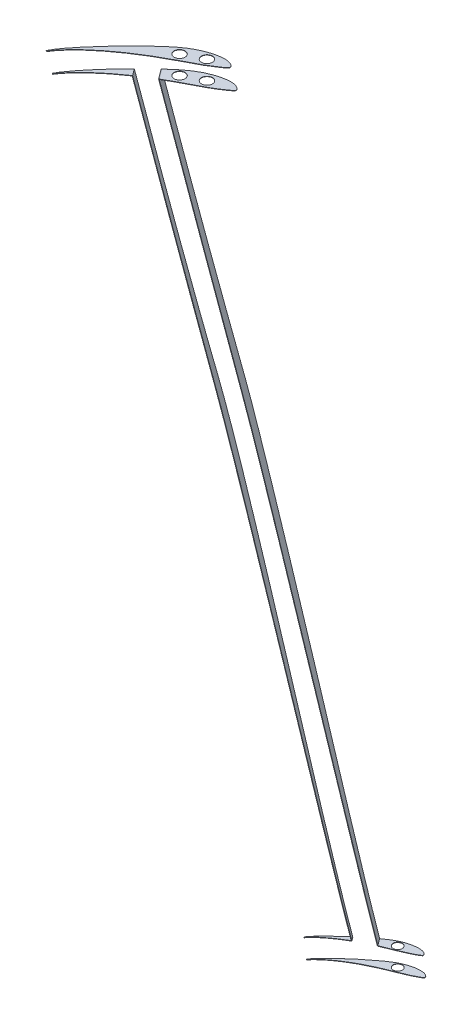
SolidWorks part; units mm, degrees
material "Thornel Mat VMA"
ref_plane "Płaszczyzna przednia" through (0, 0, 0) normal (0, 0, 1) x (1, 0, 0)
ref_plane "Płaszczyzna górna" through (0, 0, 0) normal (0, 1, 0) x (1, 0, 0)
ref_plane "Płaszczyzna prawa" through (0, 0, 0) normal (1, 0, 0) x (0, 0, -1)
sketch "Szkic1" plane through (0, 700, 0) normal (0, 1, 0) x (1, 0, 0)
  line L1 (-469.1512, -367.5434) -> (-468.754, -367.81)
  line L2 (-469.1512, -367.5434) -> (-468.754, -367.81)
  spline S1 degree 3 poles (2934.6392, 1730.5691) (-451.467, -472.6179) (-487.4852, -393.6485) (-466.9474, -365.123) (-465.4843, -363.3061) (-463.7563, -361.3596) (-461.7776, -359.314) (-459.5701, -357.2008) (-457.1553, -355.0511) (-454.5622, -352.8909) (-451.8199, -350.7459) (-448.9593, -348.6392) (-446.0148, -346.5897) (-443.0211, -344.6138) (-440.0111, -342.7277) (-437.0217, -340.9383) (-434.0854, -339.2548) (-431.2362, -337.6806) (-428.5045, -336.2174) (-425.9206, -334.863) (-423.5124, -333.6111) (-421.2981, -332.4595) (-419.3013, -331.3589) (-417.5203, -330.2935) (-415.9266, -329.301) (-414.5247, -328.3906) (-413.33, -327.5701) (-412.3464, -326.8605) (-411.611, -326.237) (-411.0798, -325.7733) (-410.823, -325.2531) (-411.0233, -324.7717) (-411.3436, -324.3272) (-411.8418, -323.8959) (-412.4803, -323.5065) (-413.2563, -323.1781) (-414.1577, -322.9224) (-415.1876, -322.7716) (-416.3391, -322.7288) (-417.6073, -322.7797) (-418.9822, -322.9364) (-420.4518, -323.2021) (-422.0055, -323.5786) (-423.6313, -324.0737) (-425.3194, -324.6838) (-427.0559, -325.415) (-428.8294, -326.2693) (-430.6234, -327.2643) (-432.439, -328.3995) (-434.2696, -329.6972) (-436.1216, -331.1507) (-438.019, -332.7225) (-439.9443, -334.4145) (-441.896, -336.2055) (-443.8686, -338.0781) (-445.856, -340.0094) (-447.8437, -341.9814) (-449.8187, -343.9734) (-451.762, -345.9737) (-453.6586, -347.9688) (-455.4966, -349.9456) (-457.2622, -351.894) (-458.9469, -353.8003) (-460.5389, -355.6542) (-462.0306, -357.4425) (-463.4128, -359.1548) (-464.6773, -360.7805) (-465.8172, -362.31) (-466.8274, -363.7332) (-467.7019, -365.0426) (-468.4374, -366.23) (-480.5946, -387.92) (-453.6741, -427.6699) (2877.8906, -2556.2502) knots -0.615528 -0.615528 -0.615528 -0.615528 0.028864 0.041831 0.056714 0.073341 0.091508 0.111022 0.131662 0.153208 0.175433 0.19811 0.221011 0.243906 0.266573 0.28881 0.310405 0.331178 0.350944 0.369556 0.386865 0.402753 0.417196 0.43038 0.442363 0.453032 0.462284 0.470026 0.476177 0.48065 0.483553 0.486421 0.489953 0.494097 0.498851 0.504197 0.510125 0.516691 0.524012 0.532092 0.540898 0.550403 0.560581 0.571396 0.582828 0.59483 0.607347 0.620384 0.633969 0.6482 0.663194 0.678899 0.695227 0.712113 0.729459 0.747143 0.76501 0.782905 0.800688 0.818242 0.835449 0.852212 0.86843 0.884009 0.898855 0.912882 0.926011 0.938167 0.94929 0.959322 0.968217 0.975948 1.433508 1.433508 1.433508 1.433508 only from (-468.754, -367.81) to (-469.1512, -367.5434)
  spline S2 degree 3 poles (-468.754, -367.81) (-468.5693, -367.4945) (-468.0116, -366.601) (-466.9474, -365.123) (-465.4843, -363.3061) (-463.7563, -361.3596) (-461.7776, -359.314) (-459.5701, -357.2008) (-457.1553, -355.0511) (-454.5622, -352.8909) (-451.8199, -350.7459) (-448.9593, -348.6392) (-446.0148, -346.5897) (-443.0211, -344.6138) (-440.0111, -342.7277) (-437.0217, -340.9383) (-434.0854, -339.2548) (-431.2362, -337.6806) (-428.5045, -336.2174) (-425.9206, -334.863) (-423.5124, -333.6111) (-421.2981, -332.4595) (-419.3013, -331.3589) (-417.5203, -330.2935) (-415.9266, -329.301) (-414.5247, -328.3906) (-413.33, -327.5701) (-412.3464, -326.8605) (-411.611, -326.237) (-411.0798, -325.7733) (-410.823, -325.2531) (-411.0233, -324.7717) (-411.3436, -324.3272) (-411.8418, -323.8959) (-412.4803, -323.5065) (-413.2563, -323.1781) (-414.1577, -322.9224) (-415.1876, -322.7716) (-416.3391, -322.7288) (-417.6073, -322.7797) (-418.9822, -322.9364) (-420.4518, -323.2021) (-422.0055, -323.5786) (-423.6313, -324.0737) (-425.3194, -324.6838) (-427.0559, -325.415) (-428.8294, -326.2693) (-430.6234, -327.2643) (-432.439, -328.3995) (-434.2696, -329.6972) (-436.1216, -331.1507) (-438.019, -332.7225) (-439.9443, -334.4145) (-441.896, -336.2055) (-443.8686, -338.0781) (-445.856, -340.0094) (-447.8437, -341.9814) (-449.8187, -343.9734) (-451.762, -345.9737) (-453.6586, -347.9688) (-455.4966, -349.9456) (-457.2622, -351.894) (-458.9469, -353.8003) (-460.5389, -355.6542) (-462.0306, -357.4425) (-463.4128, -359.1548) (-464.6773, -360.7805) (-465.8172, -362.31) (-466.8274, -363.7332) (-467.7019, -365.0426) (-468.4374, -366.23) (-468.8993, -367.0541) (-469.1182, -367.4785) (-469.1512, -367.5434) knots 0.021883 0.021883 0.021883 0.021883 0.028864 0.041831 0.056714 0.073341 0.091508 0.111022 0.131662 0.153208 0.175433 0.19811 0.221011 0.243906 0.266573 0.28881 0.310405 0.331178 0.350944 0.369556 0.386865 0.402753 0.417196 0.43038 0.442363 0.453032 0.462284 0.470026 0.476177 0.48065 0.483553 0.486421 0.489953 0.494097 0.498851 0.504197 0.510125 0.516691 0.524012 0.532092 0.540898 0.550403 0.560581 0.571396 0.582828 0.59483 0.607347 0.620384 0.633969 0.6482 0.663194 0.678899 0.695227 0.712113 0.729459 0.747143 0.76501 0.782905 0.800688 0.818242 0.835449 0.852212 0.86843 0.884009 0.898855 0.912882 0.926011 0.938167 0.94929 0.959322 0.968217 0.975948 0.977339 0.977339 0.977339 0.977339
  dimension "D1" = 0
extrude "Dodanie-wyciągnięcie1" add sketch "Szkic1" along normal blind 0.2
sketch "Szkic2" plane through (0, 690, 0) normal (0, -1, 0) x (1, 0, 0)
  line L0 (-435.1547, 340.1136) -> (-439.1678, 334.7049) construction
  line L1 (-466.5168, 366.7553) -> (-466.9139, 366.4887) construction
  line L2 (-446.602, 341.9323) -> (-443.8693, 345.6152) construction
  line L3 (-435.1547, 340.1136) -> (-439.1678, 334.7049)
  line L4 (-466.5168, 366.7553) -> (-466.9139, 366.4887)
  line L5 (-446.602, 341.9323) -> (-443.8693, 345.6152)
  spline S0 degree 3 poles (-2529.6654, -1804.7759) (-503.5039, 558.2909) (-512.0423, 398.6848) (-435.7818, 331.6679) (-433.8844, 330.096) (-432.0324, 328.6425) (-430.2018, 327.3448) (-428.3861, 326.2096) (-426.5921, 325.2146) (-424.8187, 324.3603) (-423.0822, 323.6291) (-421.394, 323.019) (-419.7682, 322.5239) (-418.2145, 322.1474) (-416.745, 321.8817) (-415.3701, 321.725) (-414.1018, 321.6741) (-412.9503, 321.717) (-411.9205, 321.8677) (-411.0191, 322.1234) (-410.2431, 322.4518) (-409.6046, 322.8412) (-409.1064, 323.2725) (-408.7861, 323.717) (-408.5857, 324.1984) (-408.8425, 324.7186) (-409.3738, 325.1823) (-410.1092, 325.8058) (-411.0927, 326.5154) (-412.2874, 327.3359) (-413.6894, 328.2463) (-415.283, 329.2388) (-417.064, 330.3042) (-419.0609, 331.4049) (-421.2751, 332.5564) (-423.6833, 333.8083) (-426.2672, 335.1627) (-428.9989, 336.6259) (-431.8482, 338.2001) (-584.3312, 425.6271) (-609.8992, 727.8412) (1261.0637, 2777.1738) knots -1.704808 -1.704808 -1.704808 -1.704808 0.289665 0.306754 0.323191 0.338884 0.353778 0.367996 0.381641 0.394742 0.407303 0.419268 0.430588 0.44124 0.451188 0.460405 0.468862 0.476524 0.483395 0.4896 0.495196 0.500171 0.504508 0.508205 0.511207 0.514245 0.518927 0.525364 0.533467 0.54315 0.554317 0.566859 0.580657 0.595773 0.612402 0.630518 0.649998 0.670686 0.692427 0.715028 4.182043 4.182043 4.182043 4.182043 only from (-439.1678, 334.7049) to (-435.1547, 340.1136) construction
  spline S1 degree 3 poles (2037.7806, 2016.4522) (-456.0134, 419.5357) (-477.2721, 384.9291) (-466.2001, 365.1753) (-465.4647, 363.9879) (-464.5901, 362.6785) (-463.5799, 361.2553) (-462.44, 359.7258) (-461.1756, 358.1001) (-459.7934, 356.3878) (-458.3016, 354.5995) (-456.7097, 352.7456) (-455.0249, 350.8393) (-453.2594, 348.8909) (-451.4213, 346.9142) (-449.5248, 344.919) (-346.783, 239.1641) (-161.5356, 215.7781) (-2341.8323, -1958.6099) knots 0.354072 0.354072 0.354072 0.354072 0.788661 0.796752 0.806062 0.816562 0.828203 0.840926 0.854667 0.869348 0.884886 0.901192 0.918166 0.93571 0.953719 0.972091 0.990704 3.899342 3.899342 3.899342 3.899342 only from (-466.9139, 366.4887) to (-446.602, 341.9323) construction
  spline S2 degree 3 poles (-2655.0268, -1659.6605) (34.7968, 421.321) (-307.2247, 244.8509) (-449.5826, 349.6912) (-452.325, 351.8362) (-454.9181, 353.9964) (-457.3328, 356.1461) (-459.5403, 358.2593) (-461.519, 360.3049) (-463.247, 362.2515) (-464.7102, 364.0683) (-483.4662, 390.1191) (-455.1792, 457.9529) (2097.3927, -1187.7395) knots -3.461473 -3.461473 -3.461473 -3.461473 0.023161 0.046895 0.070157 0.092708 0.11431 0.134733 0.153747 0.17115 0.186726 0.200298 0.813692 0.813692 0.813692 0.813692 only from (-443.8693, 345.6152) to (-466.5168, 366.7553) construction
  spline S3 degree 3 poles (-439.1678, 334.7049) (-438.6749, 334.2487) (-437.547, 333.2192) (-435.7818, 331.6679) (-433.8844, 330.096) (-432.0324, 328.6425) (-430.2018, 327.3448) (-428.3861, 326.2096) (-426.5921, 325.2146) (-424.8187, 324.3603) (-423.0822, 323.6291) (-421.394, 323.019) (-419.7682, 322.5239) (-418.2145, 322.1474) (-416.745, 321.8817) (-415.3701, 321.725) (-414.1018, 321.6741) (-412.9503, 321.717) (-411.9205, 321.8677) (-411.0191, 322.1234) (-410.2431, 322.4518) (-409.6046, 322.8412) (-409.1064, 323.2725) (-408.7861, 323.717) (-408.5857, 324.1984) (-408.8425, 324.7186) (-409.3738, 325.1823) (-410.1092, 325.8058) (-411.0927, 326.5154) (-412.2874, 327.3359) (-413.6894, 328.2463) (-415.283, 329.2388) (-417.064, 330.3042) (-419.0609, 331.4049) (-421.2751, 332.5564) (-423.6833, 333.8083) (-426.2672, 335.1627) (-428.9989, 336.6259) (-431.8482, 338.2001) (-433.9095, 339.3819) (-435.0199, 340.0342) (-435.1547, 340.1136) knots 0.276246 0.276246 0.276246 0.276246 0.289665 0.306754 0.323191 0.338884 0.353778 0.367996 0.381641 0.394742 0.407303 0.419268 0.430588 0.44124 0.451188 0.460405 0.468862 0.476524 0.483395 0.4896 0.495196 0.500171 0.504508 0.508205 0.511207 0.514245 0.518927 0.525364 0.533467 0.54315 0.554317 0.566859 0.580657 0.595773 0.612402 0.630518 0.649998 0.670686 0.692427 0.715028 0.718154 0.718154 0.718154 0.718154
  spline S4 degree 3 poles (-466.9139, 366.4887) (-466.881, 366.4238) (-466.662, 365.9994) (-466.2001, 365.1753) (-465.4647, 363.9879) (-464.5901, 362.6785) (-463.5799, 361.2553) (-462.44, 359.7258) (-461.1756, 358.1001) (-459.7934, 356.3878) (-458.3016, 354.5995) (-456.7097, 352.7456) (-455.0249, 350.8393) (-453.2594, 348.8909) (-451.4213, 346.9142) (-449.5248, 344.919) (-447.9105, 343.2574) (-446.9295, 342.2628) (-446.602, 341.9323) knots 0.787205 0.787205 0.787205 0.787205 0.788661 0.796752 0.806062 0.816562 0.828203 0.840926 0.854667 0.869348 0.884886 0.901192 0.918166 0.93571 0.953719 0.972091 0.990704 1 1 1 1
  spline S5 degree 3 poles (-443.8693, 345.6152) (-444.8285, 346.2665) (-446.7546, 347.6085) (-449.5826, 349.6912) (-452.325, 351.8362) (-454.9181, 353.9964) (-457.3328, 356.1461) (-459.5403, 358.2593) (-461.519, 360.3049) (-463.247, 362.2515) (-464.7102, 364.0683) (-465.7743, 365.5463) (-466.3321, 366.4398) (-466.5168, 366.7553) knots 0 0 0 0 0.023161 0.046895 0.070157 0.092708 0.11431 0.134733 0.153747 0.17115 0.186726 0.200298 0.207605 0.207605 0.207605 0.207605
extrude "Dodanie-wyciągnięcie2" add sketch "Szkic2" along normal blind 0.2 separate body
sketch "Szkic3" plane through (-295.5385, -87.1837, 219.2858) normal (0.7814, 0.2305, -0.5798) x (-0.5561, -0.1641, -0.8147)
  line L2 (-112.4421, 394.8727) -> (-107.7185, 395.6807)
  line L3 (-141.6635, 786.0642) -> (-148.3021, 784.9287)
  line L4 (-112.4421, 394.8727) -> (-107.7185, 395.6807)
  line L5 (-141.6635, 786.0642) -> (-148.3021, 784.9287)
  spline S4 degree 3 poles (-3388.1387, 2526.076) (-255.5865, 2195.604) (-234.0003, 1468.0754) (-142.3726, 737.2976) (-140.8602, 725.3936) (-137.7813, 701.5924) (-136.2142, 689.6955) (-43.9459, -2.7103) (94.452, -676.8291) (-2928.0534, -1774.4159) knots -14.844138 -14.844138 -14.844138 -14.844138 0.25 0.25 0.5 0.5 0.75 0.75 15.052962 15.052962 15.052962 15.052962 only from (-148.3021, 784.9287) to (-129.8475, 642.1207)
  spline S5 degree 3 poles (-4096.2574, 455.0892) (-271.7159, 995.4283) (-150.3152, 820.0791) (-128.5966, 631.8675) (-128.3199, 629.3002) (-127.5319, 621.594) (-127.0617, 616.4506) (-126.1873, 606.1588) (-125.7837, 601.01) (-125.0197, 590.7093) (-124.6597, 585.5573) (-123.6231, 570.0985) (-122.9891, 559.7892) (-121.7643, 539.168) (-121.1743, 528.8561) (-119.4091, 497.9199) (-118.2435, 477.2952) (-116.3225, 446.3682) (-115.654, 436.0612) (-114.5562, 420.6076) (-114.1743, 415.4576) (-92.4744, 141.7218) (-4.0013, -122.1115) (3801.4449, -84.2329) knots -2.230311 -2.230311 -2.230311 -2.230311 0.03125 0.03125 0.0625 0.0625 0.125 0.125 0.1875 0.1875 0.25 0.25 0.375 0.375 0.5 0.5 0.75 0.75 0.875 0.875 0.9375 0.9375 4.19828 4.19828 4.19828 4.19828 only from (-129.8475, 642.1207) to (-112.4421, 394.8727)
  spline S6 degree 3 poles (3864.7422, 541.3942) (21.3943, 66.8724) (-93.8076, 231.5917) (-108.678, 405.986) (-108.8748, 408.5658) (-109.4171, 416.3085) (-109.7149, 421.4753) (-110.2397, 431.8109) (-110.4658, 436.9804) (-110.8759, 447.3211) (-111.0596, 452.4925) (-111.5775, 468.0077) (-111.8772, 478.3526) (-112.4838, 499.0422) (-112.7962, 509.3867) (-113.5077, 530.073) (-113.9042, 540.4147) (-114.7971, 561.0932) (-115.2925, 571.4303) (-116.1433, 586.9311) (-116.445, 592.0969) (-117.1003, 602.4237) (-117.4533, 607.5849) (-118.2459, 617.8999) (-118.6838, 623.0539) (-119.4693, 630.7738) (-119.753, 633.3453) (-136.9636, 772.4475) (-248.7309, 903.2695) (-4090.6219, 305.3044) knots -2.051414 -2.051414 -2.051414 -2.051414 0.03125 0.03125 0.0625 0.0625 0.125 0.125 0.1875 0.1875 0.25 0.25 0.375 0.375 0.5 0.5 0.625 0.625 0.75 0.75 0.8125 0.8125 0.875 0.875 0.9375 0.9375 0.96875 0.96875 2.629884 2.629884 2.629884 2.629884 only from (-107.7185, 395.6807) to (-121.1491, 643.6085)
  spline S7 degree 3 poles (-3842.8812, -686.314) (-26.7706, 183.142) (-84.0861, 420.839) (-125.0571, 667.2787) (-126.0285, 673.1971) (-127.9253, 685.0415) (-128.8518, 690.9674) (-130.6519, 702.8265) (-131.5256, 708.7599) (-134.0718, 726.5708) (-135.6686, 738.4598) (-202.9391, 1260.382) (-154.377, 1784.8922) (-3780.2093, 1843.6123) knots -4.956658 -4.956658 -4.956658 -4.956658 0.125 0.125 0.25 0.25 0.375 0.375 0.5 0.5 0.75 0.75 11.467767 11.467767 11.467767 11.467767 only from (-121.1491, 643.6085) to (-141.6635, 786.0642)
  spline S8 degree 3 poles (-148.3021, 784.9287) (-146.8324, 773.0194) (-145.3583, 761.1105) (-142.3726, 737.2976) (-140.8602, 725.3936) (-137.7813, 701.5924) (-136.2142, 689.6955) (-133.0441, 665.9063) (-131.4445, 654.0137) (-129.8475, 642.1207) knots 0 0 0 0 0.25 0.25 0.5 0.5 0.75 0.75 1 1 1 1
  spline S9 degree 3 poles (-129.8475, 642.1207) (-129.5038, 639.5612) (-129.1887, 636.998) (-128.5966, 631.8675) (-128.3199, 629.3002) (-127.5319, 621.594) (-127.0617, 616.4506) (-126.1873, 606.1588) (-125.7837, 601.01) (-125.0197, 590.7093) (-124.6597, 585.5573) (-123.6231, 570.0985) (-122.9891, 559.7892) (-121.7643, 539.168) (-121.1743, 528.8561) (-119.4091, 497.9199) (-118.2435, 477.2952) (-116.3225, 446.3682) (-115.654, 436.0612) (-114.5562, 420.6076) (-114.1743, 415.4576) (-113.3581, 405.1615) (-112.9253, 400.0152) (-112.4421, 394.8727) knots 0 0 0 0 0.03125 0.03125 0.0625 0.0625 0.125 0.125 0.1875 0.1875 0.25 0.25 0.375 0.375 0.5 0.5 0.75 0.75 0.875 0.875 0.9375 0.9375 1 1 1 1
  spline S10 degree 3 poles (-107.7185, 395.6807) (-107.9958, 398.2534) (-108.2383, 400.8299) (-108.678, 405.986) (-108.8748, 408.5658) (-109.4171, 416.3085) (-109.7149, 421.4753) (-110.2397, 431.8109) (-110.4658, 436.9804) (-110.8759, 447.3211) (-111.0596, 452.4925) (-111.5775, 468.0077) (-111.8772, 478.3526) (-112.4838, 499.0422) (-112.7962, 509.3867) (-113.5077, 530.073) (-113.9042, 540.4147) (-114.7971, 561.0932) (-115.2925, 571.4303) (-116.1433, 586.9311) (-116.445, 592.0969) (-117.1003, 602.4237) (-117.4533, 607.5849) (-118.2459, 617.8999) (-118.6838, 623.0539) (-119.4693, 630.7738) (-119.753, 633.3453) (-120.3886, 638.4823) (-120.7399, 641.0489) (-121.1491, 643.6085) knots 0 0 0 0 0.03125 0.03125 0.0625 0.0625 0.125 0.125 0.1875 0.1875 0.25 0.25 0.375 0.375 0.5 0.5 0.625 0.625 0.75 0.75 0.8125 0.8125 0.875 0.875 0.9375 0.9375 0.96875 0.96875 1 1 1 1
  spline S11 degree 3 poles (-121.1491, 643.6085) (-122.0958, 649.531) (-123.0899, 655.4458) (-125.0571, 667.2787) (-126.0285, 673.1971) (-127.9253, 685.0415) (-128.8518, 690.9674) (-130.6519, 702.8265) (-131.5256, 708.7599) (-134.0718, 726.5708) (-135.6686, 738.4598) (-138.7353, 762.2532) (-140.2065, 774.1579) (-141.6635, 786.0642) knots 0 0 0 0 0.125 0.125 0.25 0.25 0.375 0.375 0.5 0.5 0.75 0.75 1 1 1 1
  dimension "D1" = 0
extrude "Dodanie-wyciągnięcie3" add sketch "Szkic3" along normal blind 0.2
sketch "Szkic4" plane through (-303.3529, -89.489, 225.084) normal (-0.7814, -0.2305, 0.5798) x (0.5561, 0.1641, 0.8147)
  line L2 (108.4467, 397.9596) -> (111.0458, 397.515)
  line L3 (147.9379, 787.3945) -> (143.4176, 788.1677)
  line L4 (108.4467, 397.9596) -> (111.0458, 397.515)
  line L5 (147.9379, 787.3945) -> (143.4176, 788.1677)
  spline S4 degree 3 poles (3819.9224, 1758.5701) (145.1756, 1747.968) (202.4517, 1242.3767) (137.4087, 740.5652) (135.7951, 728.6783) (132.3252, 704.9414) (130.4671, 693.09) (127.4484, 675.3529) (126.4039, 669.4474) (48.3954, 244.3582) (-221.349, -140.1189) (3463.6319, -1236.5723) knots -10.046224 -10.046224 -10.046224 -10.046224 0.25 0.25 0.5 0.5 0.75 0.75 0.875 0.875 9.758208 9.758208 9.758208 9.758208 only from (143.4176, 788.1677) to (121.971, 645.8714)
  spline S5 degree 3 poles (4027.1211, -131.9607) (290.7381, 904.5626) (142.2323, 779.372) (120.2597, 635.6548) (119.9105, 633.0895) (118.9521, 625.3821) (118.4303, 620.2275) (117.5202, 609.9146) (117.1333, 604.7541) (116.447, 594.428) (116.1481, 589.2623) (115.3445, 573.7599) (114.9313, 563.4178) (114.2335, 542.7259) (113.9508, 532.3779) (113.4362, 511.681) (113.2049, 501.3319) (112.7101, 480.6344) (112.4484, 470.2859) (111.9568, 454.7666) (111.7762, 449.594) (111.363, 439.2508) (111.1306, 434.0796) (110.5835, 423.7437) (110.2697, 418.5787) (109.6924, 410.8388) (109.4819, 408.2602) (94.3598, 243.2902) (-21.0417, 88.1668) (-3865.9641, 202.7799) knots -1.691994 -1.691994 -1.691994 -1.691994 0.03125 0.03125 0.0625 0.0625 0.125 0.125 0.1875 0.1875 0.25 0.25 0.375 0.375 0.5 0.5 0.625 0.625 0.75 0.75 0.8125 0.8125 0.875 0.875 0.9375 0.9375 0.96875 0.96875 2.938175 2.938175 2.938175 2.938175 only from (121.971, 645.8714) to (108.4467, 397.9596)
  spline S6 degree 3 poles (-3841.6364, 196.9477) (0.636, -42.0712) (93.2692, 182.7231) (112.9151, 418.0854) (113.3059, 423.2348) (114.4128, 438.6866) (115.0654, 448.9937) (116.3139, 469.6114) (116.9074, 479.922) (118.0822, 500.544) (118.6622, 510.8555) (119.8416, 531.4772) (120.4405, 541.7876) (121.6954, 562.4049) (122.3503, 572.7124) (123.4238, 588.1653) (123.7971, 593.3149) (124.5898, 603.6101) (125.009, 608.7556) (125.9191, 619.0403) (126.4091, 624.1796) (127.2366, 631.8802) (127.5281, 634.4457) (148.9303, 809.3493) (269.0666, 972.9023) (4101.9173, 807.0833) knots -2.733603 -2.733603 -2.733603 -2.733603 0.0625 0.0625 0.125 0.125 0.25 0.25 0.375 0.375 0.5 0.5 0.625 0.625 0.75 0.75 0.8125 0.8125 0.875 0.875 0.9375 0.9375 0.96875 0.96875 3.069611 3.069611 3.069611 3.069611 only from (111.0458, 397.515) to (128.8605, 644.693)
  spline S7 degree 3 poles (3346.1984, -1352.7492) (-91.0102, -344.8348) (60.8853, 162.23) (135.644, 692.2026) (137.2794, 704.0886) (140.4513, 727.8739) (141.989, 739.7729) (221.9012, 1371.8225) (214.0163, 2002.7173) (3583.4617, 2212.9404) knots -10.652425 -10.652425 -10.652425 -10.652425 0.25 0.25 0.5 0.5 0.75 0.75 13.774784 13.774784 13.774784 13.774784 only from (128.8605, 644.693) to (147.9379, 787.3945)
  spline S8 degree 3 poles (143.4176, 788.1677) (141.9631, 776.261) (140.4924, 764.3562) (137.4087, 740.5652) (135.7951, 728.6783) (132.3252, 704.9414) (130.4671, 693.09) (127.4484, 675.3529) (126.4039, 669.4474) (124.2389, 657.6502) (123.1183, 651.7584) (121.971, 645.8714) knots 0 0 0 0 0.25 0.25 0.5 0.5 0.75 0.75 0.875 0.875 1 1 1 1
  spline S9 degree 3 poles (121.971, 645.8714) (121.4755, 643.329) (121.0424, 640.7744) (120.2597, 635.6548) (119.9105, 633.0895) (118.9521, 625.3821) (118.4303, 620.2275) (117.5202, 609.9146) (117.1333, 604.7541) (116.447, 594.428) (116.1481, 589.2623) (115.3445, 573.7599) (114.9313, 563.4178) (114.2335, 542.7259) (113.9508, 532.3779) (113.4362, 511.681) (113.2049, 501.3319) (112.7101, 480.6344) (112.4484, 470.2859) (111.9568, 454.7666) (111.7762, 449.594) (111.363, 439.2508) (111.1306, 434.0796) (110.5835, 423.7437) (110.2697, 418.5787) (109.6924, 410.8388) (109.4819, 408.2602) (109.0095, 403.1066) (108.748, 400.5317) (108.4467, 397.9596) knots 0 0 0 0 0.03125 0.03125 0.0625 0.0625 0.125 0.125 0.1875 0.1875 0.25 0.25 0.375 0.375 0.5 0.5 0.625 0.625 0.75 0.75 0.8125 0.8125 0.875 0.875 0.9375 0.9375 0.96875 0.96875 1 1 1 1
  spline S10 degree 3 poles (111.0458, 397.515) (111.5898, 402.6504) (112.056, 407.7936) (112.9151, 418.0854) (113.3059, 423.2348) (114.4128, 438.6866) (115.0654, 448.9937) (116.3139, 469.6114) (116.9074, 479.922) (118.0822, 500.544) (118.6622, 510.8555) (119.8416, 531.4772) (120.4405, 541.7876) (121.6954, 562.4049) (122.3503, 572.7124) (123.4238, 588.1653) (123.7971, 593.3149) (124.5898, 603.6101) (125.009, 608.7556) (125.9191, 619.0403) (126.4091, 624.1796) (127.2366, 631.8802) (127.5281, 634.4457) (128.1555, 639.5728) (128.4911, 642.1344) (128.8605, 644.693) knots 0 0 0 0 0.0625 0.0625 0.125 0.125 0.25 0.25 0.375 0.375 0.5 0.5 0.625 0.625 0.75 0.75 0.8125 0.8125 0.875 0.875 0.9375 0.9375 0.96875 0.96875 1 1 1 1
  spline S11 degree 3 poles (128.8605, 644.693) (130.575, 656.5678) (132.2923, 668.4422) (135.644, 692.2026) (137.2794, 704.0886) (140.4513, 727.8739) (141.989, 739.7729) (144.9989, 763.5793) (146.4721, 775.4864) (147.9379, 787.3945) knots 0 0 0 0 0.25 0.25 0.5 0.5 0.75 0.75 1 1 1 1
  dimension "D1" = 0
extrude "Dodanie-wyciągnięcie4" add sketch "Szkic4" along normal blind 0.2
sketch "Szkic5" plane through (0, 300, 0) normal (0, -1, 0) x (1, 0, 0)
  line L1 (-367.7235, 326.6209) -> (-367.9654, 326.4189)
  line L2 (-367.7235, 326.6209) -> (-367.9654, 326.4189)
  spline S1 degree 3 poles (2741.8325, 2841.2819) (-357.0072, 375.4917) (-378.2449, 340.9307) (-367.4072, 325.6075) (-366.8435, 324.8801) (-366.1803, 324.0823) (-365.4204, 323.2194) (-364.5681, 322.2957) (-363.6277, 321.3176) (-362.6041, 320.2908) (-361.5035, 319.2218) (-360.3327, 318.1167) (-359.0975, 316.9836) (-357.8065, 315.8286) (-356.466, 314.6599) (-355.0859, 313.4832) (-353.6748, 312.3064) (-352.2436, 311.1371) (-350.8053, 309.9819) (-349.3701, 308.8533) (-347.9486, 307.7622) (-346.5465, 306.7231) (-345.1684, 305.747) (-343.8169, 304.8478) (-342.5033, 304.0229) (-341.2145, 303.2987) (-339.9466, 302.6799) (-338.7026, 302.1515) (-337.4818, 301.7139) (-336.2936, 301.3544) (-335.1454, 301.0708) (-334.0461, 300.8584) (-333.0021, 300.7187) (-332.0209, 300.6458) (-331.1092, 300.6379) (-330.2747, 300.6919) (-329.5231, 300.7992) (-328.8587, 300.9689) (-328.2857, 301.1985) (-327.7999, 301.4672) (-327.4083, 301.7663) (-327.1116, 302.0832) (-326.9323, 302.3965) (-326.8342, 302.7258) (-327.0383, 303.0489) (-327.4183, 303.3162) (-327.9431, 303.674) (-328.6364, 304.0713) (-329.4758, 304.5266) (-330.4571, 305.0266) (-331.5696, 305.5671) (-332.81, 306.1426) (-334.1942, 306.7263) (-335.7243, 307.3283) (-337.3885, 307.9828) (-339.1748, 308.6922) (-341.0655, 309.4629) (-343.0408, 310.2981) (-345.0807, 311.199) (-347.1627, 312.1656) (-349.2649, 313.1942) (-351.3626, 314.2826) (-353.433, 315.4228) (-355.4524, 316.6061) (-357.3971, 317.8228) (-359.2449, 319.0596) (-360.9752, 320.3019) (-362.5672, 321.5345) (-364.0046, 322.7386) (-365.2709, 323.895) (-366.3547, 324.9847) (-383.9627, 344.7107) (-357.649, 412.9936) (3220.5049, -1438.1305) knots -0.549735 -0.549735 -0.549735 -0.549735 0.001456 0.009547 0.018857 0.029357 0.040998 0.053721 0.067462 0.082143 0.097681 0.113987 0.130961 0.148505 0.166514 0.184886 0.203499 0.222228 0.240928 0.259436 0.277591 0.295265 0.312354 0.328791 0.344484 0.359378 0.373596 0.387241 0.400342 0.412903 0.424868 0.436187 0.446839 0.456788 0.466004 0.474462 0.482123 0.488995 0.4952 0.500796 0.505771 0.510108 0.513805 0.516806 0.519845 0.524527 0.530964 0.539067 0.54875 0.559917 0.572459 0.586257 0.601373 0.618002 0.636118 0.655598 0.676285 0.698027 0.720628 0.743902 0.767626 0.791588 0.815556 0.839291 0.862552 0.885103 0.906705 0.927129 0.946142 0.963545 0.979122 0.992693 1.766879 1.766879 1.766879 1.766879 only from (-367.9654, 326.4189) to (-367.7235, 326.6209)
  spline S2 degree 3 poles (-367.9654, 326.4189) (-367.9393, 326.3786) (-367.7666, 326.1156) (-367.4072, 325.6075) (-366.8435, 324.8801) (-366.1803, 324.0823) (-365.4204, 323.2194) (-364.5681, 322.2957) (-363.6277, 321.3176) (-362.6041, 320.2908) (-361.5035, 319.2218) (-360.3327, 318.1167) (-359.0975, 316.9836) (-357.8065, 315.8286) (-356.466, 314.6599) (-355.0859, 313.4832) (-353.6748, 312.3064) (-352.2436, 311.1371) (-350.8053, 309.9819) (-349.3701, 308.8533) (-347.9486, 307.7622) (-346.5465, 306.7231) (-345.1684, 305.747) (-343.8169, 304.8478) (-342.5033, 304.0229) (-341.2145, 303.2987) (-339.9466, 302.6799) (-338.7026, 302.1515) (-337.4818, 301.7139) (-336.2936, 301.3544) (-335.1454, 301.0708) (-334.0461, 300.8584) (-333.0021, 300.7187) (-332.0209, 300.6458) (-331.1092, 300.6379) (-330.2747, 300.6919) (-329.5231, 300.7992) (-328.8587, 300.9689) (-328.2857, 301.1985) (-327.7999, 301.4672) (-327.4083, 301.7663) (-327.1116, 302.0832) (-326.9323, 302.3965) (-326.8342, 302.7258) (-327.0383, 303.0489) (-327.4183, 303.3162) (-327.9431, 303.674) (-328.6364, 304.0713) (-329.4758, 304.5266) (-330.4571, 305.0266) (-331.5696, 305.5671) (-332.81, 306.1426) (-334.1942, 306.7263) (-335.7243, 307.3283) (-337.3885, 307.9828) (-339.1748, 308.6922) (-341.0655, 309.4629) (-343.0408, 310.2981) (-345.0807, 311.199) (-347.1627, 312.1656) (-349.2649, 313.1942) (-351.3626, 314.2826) (-353.433, 315.4228) (-355.4524, 316.6061) (-357.3971, 317.8228) (-359.2449, 319.0596) (-360.9752, 320.3019) (-362.5672, 321.5345) (-364.0046, 322.7386) (-365.2709, 323.895) (-366.3547, 324.9847) (-367.1537, 325.8799) (-367.5808, 326.4269) (-367.7235, 326.6209) knots 0 0 0 0 0.001456 0.009547 0.018857 0.029357 0.040998 0.053721 0.067462 0.082143 0.097681 0.113987 0.130961 0.148505 0.166514 0.184886 0.203499 0.222228 0.240928 0.259436 0.277591 0.295265 0.312354 0.328791 0.344484 0.359378 0.373596 0.387241 0.400342 0.412903 0.424868 0.436187 0.446839 0.456788 0.466004 0.474462 0.482123 0.488995 0.4952 0.500796 0.505771 0.510108 0.513805 0.516806 0.519845 0.524527 0.530964 0.539067 0.54875 0.559917 0.572459 0.586257 0.601373 0.618002 0.636118 0.655598 0.676285 0.698027 0.720628 0.743902 0.767626 0.791588 0.815556 0.839291 0.862552 0.885103 0.906705 0.927129 0.946142 0.963545 0.979122 0.992693 1 1 1 1
  dimension "D1" = 0
extrude "Dodanie-wyciągnięcie5" add sketch "Szkic5" along normal blind 0.2 separate body
sketch "Szkic6" plane through (0, 310, 0) normal (0, 1, 0) x (1, 0, 0)
  line L0 (-368.9566, -326.8036) -> (-368.713, -327.0065) construction
  line L1 (-354.0718, -315.5577) -> (-355.643, -313.44) construction
  line L2 (-347.5887, -307.0485) -> (-344.7331, -310.897) construction
  line L3 (-368.9566, -326.8036) -> (-368.713, -327.0065)
  line L4 (-354.0718, -315.5577) -> (-355.643, -313.44)
  line L5 (-347.5887, -307.0485) -> (-344.7331, -310.897)
  spline S0 degree 3 poles (1528.9399, -2649.2264) (-379.4372, -405.6241) (-388.6704, -347.7446) (-366.6504, -324.6524) (-366.092, -324.1131) (-364.3719, -322.5468) (-363.1667, -321.5699) (-360.6776, -319.7067) (-359.39, -318.82) (-257.5083, -253.1797) (-15.9111, -438.2655) (-1503.4711, 2440.4521) knots -4.87225 -4.87225 -4.87225 -4.87225 0.125 0.125 0.25 0.25 0.5 0.5 0.75 0.75 19.904994 19.904994 19.904994 19.904994 only from (-368.713, -327.0065) to (-354.0718, -315.5577) construction
  spline S1 degree 3 poles (-2059.0443, 2137.9286) (-29.1207, -307.5144) (-270.5659, -230.7134) (-363.8041, -320.8409) (-364.9161, -321.961) (-366.5173, -323.7048) (-367.0397, -324.2958) (-367.7922, -325.209) (-368.0379, -325.5178) (-384.6452, -347.5911) (-362.5981, -397.7238) (2113.1015, -2010.3916) knots -19.835789 -19.835789 -19.835789 -19.835789 0.5 0.5 0.75 0.75 0.875 0.875 0.9375 0.9375 5.243706 5.243706 5.243706 5.243706 only from (-355.643, -313.44) to (-368.9566, -326.8036) construction
  spline S2 degree 3 poles (840.81, -3057.0693) (-500.9075, -451.2273) (-433.7129, -346.7792) (-339.1092, -308.5397) (-338.2995, -308.2177) (-336.6794, -307.5756) (-335.8676, -307.2589) (-334.658, -306.7639) (-334.2564, -306.5951) (-333.458, -306.2453) (-333.0616, -306.0637) (-331.8793, -305.5061) (-331.0974, -305.1218) (-329.941, -304.5125) (-329.5579, -304.304) (-328.8019, -303.8695) (-328.4337, -303.6338) (-327.9923, -303.3146) (-327.9074, -303.2468) (-327.7969, -303.125) (-327.763, -303.0819) (-327.7071, -302.9875) (-327.6853, -302.9365) (-327.668, -302.8279) (-327.6735, -302.7728) (-327.6983, -302.6667) (-327.7171, -302.616) (-327.7804, -302.4665) (-327.8342, -302.3712) (-328.0196, -302.1074) (-328.177, -301.9545) (-328.5114, -301.6863) (-328.6917, -301.5704) (-329.2616, -301.2628) (-329.6637, -301.1172) (-330.2875, -300.9674) (-330.5, -300.9283) (-330.9244, -300.8673) (-331.1367, -300.845) (-332.1987, -300.763) (-333.0496, -300.7961) (-334.7529, -300.9832) (-335.5871, -301.1387) (-337.2307, -301.5364) (-338.0398, -301.7799) (-339.236, -302.2063) (-339.6317, -302.3592) (-340.4167, -302.6874) (-340.8072, -302.8627) (-341.9591, -303.4132) (-342.7002, -303.8167) (-344.1409, -304.6802) (-344.8432, -305.1366) (-401.6988, -343.4448) (-383.1568, -482.9387) (-2279.1745, 1982.8075) knots -7.131918 -7.131918 -7.131918 -7.131918 0.125 0.125 0.1875 0.1875 0.25 0.25 0.28125 0.28125 0.3125 0.3125 0.375 0.375 0.40625 0.40625 0.4375 0.4375 0.445312 0.445312 0.449219 0.449219 0.453125 0.453125 0.457031 0.457031 0.460937 0.460937 0.46875 0.46875 0.484375 0.484375 0.5 0.5 0.53125 0.53125 0.546875 0.546875 0.5625 0.5625 0.625 0.625 0.6875 0.6875 0.75 0.75 0.78125 0.78125 0.8125 0.8125 0.875 0.875 0.9375 0.9375 5.995271 5.995271 5.995271 5.995271 only from (-344.7331, -310.897) to (-347.5887, -307.0485) construction
  spline S3 degree 3 poles (-368.713, -327.0065) (-368.2433, -326.3651) (-367.7251, -325.7794) (-366.6504, -324.6524) (-366.092, -324.1131) (-364.3719, -322.5468) (-363.1667, -321.5699) (-360.6776, -319.7067) (-359.39, -318.82) (-356.7648, -317.1287) (-355.4282, -316.3256) (-354.0718, -315.5577) knots 0 0 0 0 0.125 0.125 0.25 0.25 0.5 0.5 0.75 0.75 1 1 1 1
  spline S4 degree 3 poles (-355.643, -313.44) (-358.0522, -315.4685) (-360.4071, -317.5573) (-363.8041, -320.8409) (-364.9161, -321.961) (-366.5173, -323.7048) (-367.0397, -324.2958) (-367.7922, -325.209) (-368.0379, -325.5178) (-368.5131, -326.1494) (-368.7426, -326.4712) (-368.9566, -326.8036) knots 0 0 0 0 0.5 0.5 0.75 0.75 0.875 0.875 0.9375 0.9375 1 1 1 1
  spline S5 degree 3 poles (-344.7331, -310.897) (-343.1404, -310.192) (-341.5326, -309.5193) (-339.1092, -308.5397) (-338.2995, -308.2177) (-336.6794, -307.5756) (-335.8676, -307.2589) (-334.658, -306.7639) (-334.2564, -306.5951) (-333.458, -306.2453) (-333.0616, -306.0637) (-331.8793, -305.5061) (-331.0974, -305.1218) (-329.941, -304.5125) (-329.5579, -304.304) (-328.8019, -303.8695) (-328.4337, -303.6338) (-327.9923, -303.3146) (-327.9074, -303.2468) (-327.7969, -303.125) (-327.763, -303.0819) (-327.7071, -302.9875) (-327.6853, -302.9365) (-327.668, -302.8279) (-327.6735, -302.7728) (-327.6983, -302.6667) (-327.7171, -302.616) (-327.7804, -302.4665) (-327.8342, -302.3712) (-328.0196, -302.1074) (-328.177, -301.9545) (-328.5114, -301.6863) (-328.6917, -301.5704) (-329.2616, -301.2628) (-329.6637, -301.1172) (-330.2875, -300.9674) (-330.5, -300.9283) (-330.9244, -300.8673) (-331.1367, -300.845) (-332.1987, -300.763) (-333.0496, -300.7961) (-334.7529, -300.9832) (-335.5871, -301.1387) (-337.2307, -301.5364) (-338.0398, -301.7799) (-339.236, -302.2063) (-339.6317, -302.3592) (-340.4167, -302.6874) (-340.8072, -302.8627) (-341.9591, -303.4132) (-342.7002, -303.8167) (-344.1409, -304.6802) (-344.8432, -305.1366) (-346.2312, -306.0718) (-346.9138, -306.5549) (-347.5887, -307.0485) knots 0 0 0 0 0.125 0.125 0.1875 0.1875 0.25 0.25 0.28125 0.28125 0.3125 0.3125 0.375 0.375 0.40625 0.40625 0.4375 0.4375 0.445312 0.445312 0.449219 0.449219 0.453125 0.453125 0.457031 0.457031 0.460937 0.460937 0.46875 0.46875 0.484375 0.484375 0.5 0.5 0.53125 0.53125 0.546875 0.546875 0.5625 0.5625 0.625 0.625 0.6875 0.6875 0.75 0.75 0.78125 0.78125 0.8125 0.8125 0.875 0.875 0.9375 0.9375 1 1 1 1
extrude "Dodanie-wyciągnięcie6" add sketch "Szkic6" along normal blind 0.2
sketch "Szkic7" plane through (0, 700.2, 0) normal (0, 1, 0) x (1, 0, 0)
  circle A0 centre (-421.0901, -327.7251) radius 3
  circle A1 centre (-431.0397, -332.7742) radius 3
  dimension "D1" = 6
  dimension "D2" = 6
extrude "Wytnij-wyciągnięcie1" cut sketch "Szkic7" against normal blind 12
sketch "Szkic8" plane through (0, 310.2, 0) normal (0, 1, 0) x (1, 0, 0)
  circle A0 centre (-339.083, -305.4298) radius 2.5
  dimension "D1" = 5
extrude "Wytnij-wyciągnięcie2" cut sketch "Szkic8" against normal blind 12
